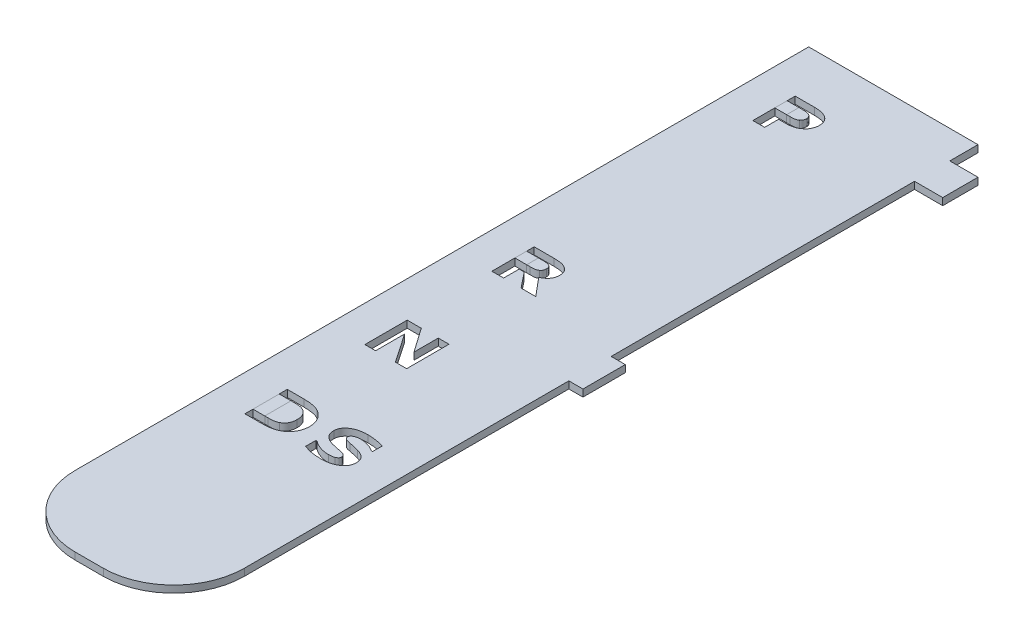
SolidWorks part; units mm, degrees
ref_plane "Front Plane" through (0, 0, 0) normal (0, 0, 1) x (1, 0, 0)
ref_plane "Top Plane" through (0, 0, 0) normal (0, 1, 0) x (1, 0, 0)
ref_plane "Right Plane" through (0, 0, 0) normal (1, 0, 0) x (0, 0, -1)
sketch "Sketch1" plane through (0, 0, 0) normal (0, 1, 0) x (1, 0, 0)
  line L1 (-12, 52) -> (12, 52)
  line L2 (-12, 52) -> (-12, -52)
  line L3 (-2, -62) -> (2, -62)
  line L4 (12, 52) -> (12, 48)
  line L5 (0, -62) -> (0, 0) construction
  line L6 (-12, 0) -> (0, 0) construction
  line L11 (16, 48) -> (16, 43)
  line L12 (16, 43) -> (12, 43)
  line L13 (13, 0) -> (14, 0)
  line L15 (12, -6) -> (14, -6)
  line L16 (14, 0) -> (14, -6)
  line L17 (13, -6) -> (13, 0) construction
  line L18 (9.7634, -3) -> (14, -3) construction
  line L19 (12, -6) -> (12, -52)
  line L23 (-7.75, 39) -> (-1.4433, 39) construction
  line L25 (-7.75, -16) -> (1.5413, -16) construction
  line L26 (-7.75, 2) -> (3.1861, 2) construction
  line L27 (-7.75, -33) -> (5.432, -33) construction
  line L29 (12, 48) -> (16, 48)
  line L30 (12, 43) -> (12, 42)
  line L32 (12, 42) -> (12, 0)
  line L33 (12, 0) -> (13, 0)
  arc A0 (2, -62) -> (12, -52) centre (2, -52) ccw
  arc A1 (-12, -52) -> (-2, -62) centre (-2, -52) ccw
  text T0 "<b>P</b>" font "Century Gothic" height 6
  text T1 "<b>R</b>" font "Century Gothic" height 6
  text T2 "<b>N</b>" font "Century Gothic" height 6
  text T3 "<b>DS</b>" font "Century Gothic" height 6
  point P27 (12, -62)
  point P96 (13, -3)
  point P132 (14, 45)
  point P135 (-0.152, 51.0703)
  point P296 (0, 0)
  dimension "D9" = 10
  dimension "D11" = 10
  dimension "D1" = 24
  dimension "D2" = 6
  dimension "D3" = 4
  dimension "D4" = 5
  dimension "D5" = 13
  dimension "D6" = 85
  dimension "D7" = 50
  dimension "D8" = 68
  dimension "D10" = 46
  dimension "D12" = 4.25
  dimension "D13" = 114
  dimension "D16" = 2
sketch "Sketch2" plane through (0, 0, 0) normal (0, 1, 0) x (1, 0, 0)
  line L0 (-7.75, 39) -> (-1.4433, 39) construction
  line L1 (-7.75, 2) -> (3.1861, 2) construction
  line L2 (-7.75, -16) -> (1.5413, -16) construction
  line L3 (-7.75, -33) -> (5.432, -33) construction
  text T0 "<b>P</b>" font "Verdana" height 6
  text T1 "<b>R</b>" font "Verdana" height 6
  text T2 "<b>N</b>" font "Verdana" height 6
  text T3 "<b>DS</b>" font "Verdana" height 6
extrude "Boss-Extrude6" add sketch "Sketch1" along normal blind 1
extrude "Cut-Extrude2" cut sketch "Sketch2" along normal blind 1
sketch "Sketch3" plane through (0, 1, 0) normal (0, 1, 0) x (1, 0, 0)
  line L0 (-6.9146, 39) -> (-6.9146, 45) construction
  line L1 (-5.2437, 43.8608) -> (-6.9146, 43.8608)
  line L2 (-5.2437, 43.8608) -> (-5.2437, 42.1139)
  line L3 (-5.2437, 42.1139) -> (-6.9146, 42.1139)
  line L4 (-6.9146, 43.8608) -> (-6.9146, 42.1139)
  line L5 (-6.0791, 42.1139) -> (-6.0791, 43.8608) construction
  line L6 (-5.2437, 42.9873) -> (-6.9146, 42.9873) construction
  line L7 (-6.9146, 2) -> (-6.9146, 8) construction
  line L8 (-5.2437, 6.9367) -> (-6.9146, 6.9367)
  line L9 (-5.2437, 6.9367) -> (-5.2437, 5.2658)
  line L10 (-5.2437, 5.2658) -> (-6.9146, 5.2658)
  line L11 (-6.9146, 6.9367) -> (-6.9146, 5.2658)
  line L12 (-6.0791, 5.2658) -> (-6.0791, 6.9367) construction
  line L13 (-5.2437, 6.1013) -> (-6.9146, 6.1013) construction
  line L14 (-6.9146, -33) -> (-6.9146, -27) construction
  line L15 (-5.2437, -28.1392) -> (-6.9146, -28.1392)
  line L16 (-5.2437, -28.1392) -> (-5.2437, -31.8608)
  line L17 (-5.2437, -31.8608) -> (-6.9146, -31.8608)
  line L18 (-6.9146, -28.1392) -> (-6.9146, -31.8608)
  line L19 (-6.0791, -31.8608) -> (-6.0791, -28.1392) construction
  line L20 (-5.2437, -30) -> (-6.9146, -30) construction
  point P204 (-6.0791, 42.9873)
  point P312 (-6.0791, 6.1013)
  point P548 (-6.0791, -30)
extrude "Boss-Extrude7" add sketch "Sketch3" against normal blind 1 separate body
